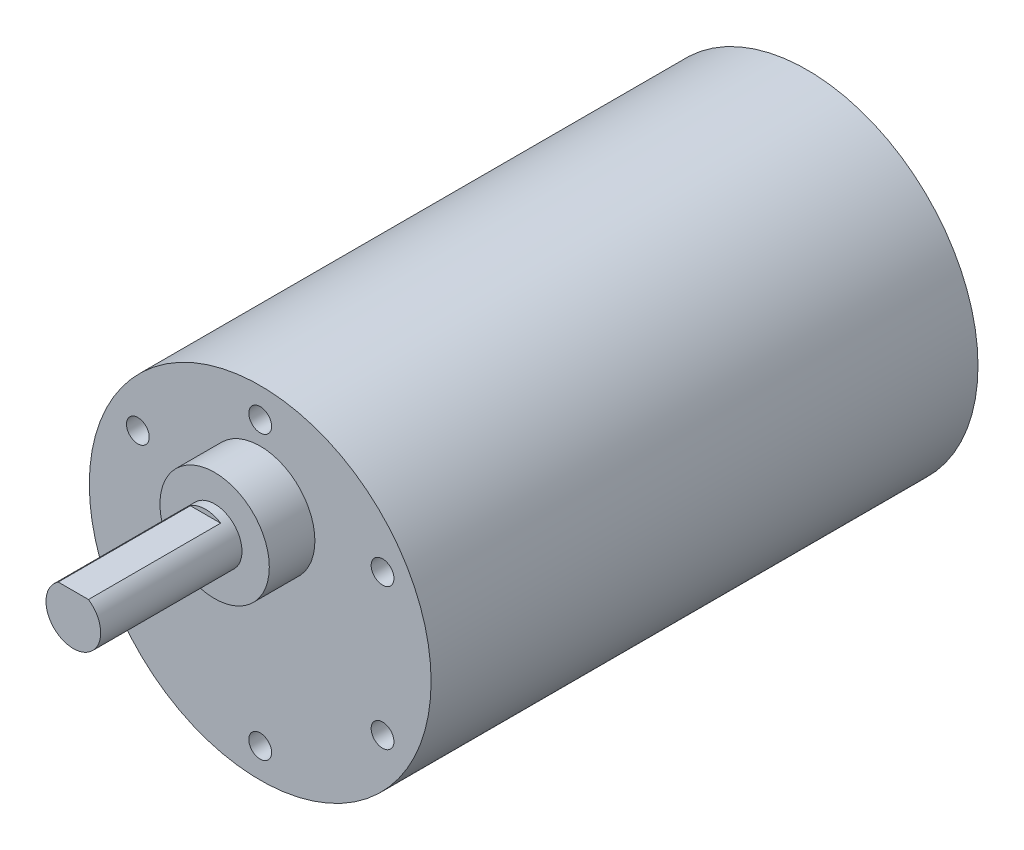
SolidWorks part; units mm, degrees
ref_plane "前视基准面" through (0, 0, 0) normal (0, 0, 1) x (1, 0, 0)
ref_plane "上视基准面" through (0, 0, 0) normal (0, 1, 0) x (1, 0, 0)
ref_plane "右视基准面" through (0, 0, 0) normal (1, 0, 0) x (0, 0, -1)
sketch "草图1" plane through (0, 0, 0) normal (0, 0, 1) x (1, 0, 0)
  line L0 (0, 0) -> (0, 16.5515) construction
  circle A0 centre (0, 0) radius 18.75
  dimension "D1" = 37.5
extrude "凸台-拉伸1" add sketch "草图1" along normal blind 60
sketch "草图2" plane through (0, 0, 60) normal (0, 0, 1) x (1, 0, 0)
  line L0 (0, 0) -> (0, 14.3743) construction
  circle A0 centre (0, 7) radius 6
  dimension "D2" = 12
  dimension "D1" = 7
extrude "凸台-拉伸2" add sketch "草图2" along normal blind 5
sketch "草图3" plane through (0, 0, 65) normal (0, 0, 1) x (1, 0, 0)
  circle A0 centre (0, 7) radius 3
  dimension "D1" = 6
extrude "凸台-拉伸3" add sketch "草图3" along normal blind 15.5
sketch "草图4" plane through (0, 0, 80.5) normal (0, 0, 1) x (1, 0, 0)
  line L1 (-3.708, 11.4083) -> (3.6239, 11.4083)
  line L2 (-3.708, 11.4083) -> (-3.708, 9.5)
  line L3 (-3.708, 9.5) -> (3.6239, 9.5)
  line L4 (3.6239, 11.4083) -> (3.6239, 9.5)
  circle A0 centre (0, 7) radius 3 construction
  dimension "D1" = 2.5
extrude "切除-拉伸1" cut sketch "草图4" against normal blind 14.5
hole_wizard "M3 螺纹孔1" positions "草图5" profile "草图6" tap size "M3" standard "ISO"
sketch "草图5" plane through (0, 0, 60) normal (0, 0, 1) x (1, 0, 0)
  line L0 (0, 0) -> (0, 19.2926) construction
  circle A0 centre (0, 0) radius 15.5 construction
  point P0 (0, 15.5)
  dimension "D1" = 31
cosmetic thread "孔螺蚊线1" parameters "D2"=3
sketch "草图6" plane through (0, 15.5, 60) normal (1, 0, 0) x (0, -1, 0)
  line L0 (0, 0) -> (0, 8.2511)
  line L1 (0, 8.2511) -> (1.25, 7.5)
  line L2 (1.25, 7.5) -> (1.25, 0)
  line L5 (1.25, 0) -> (0, 0)
  line L10 (0, 8.2511) -> (-1.25, 7.5) construction
  line L11 (0, -6.35) -> (0, 107.95) construction
  dimension "螺纹孔钻头直径" = 2.5
  dimension "螺纹孔钻头深度" = 7.5
  dimension "导头角度" = 118
pattern_circular "阵列(圆周)1" count 6 over 360 about axis through (0, 0, 0) along (0, 0, 1) of "M3 螺纹孔1"
